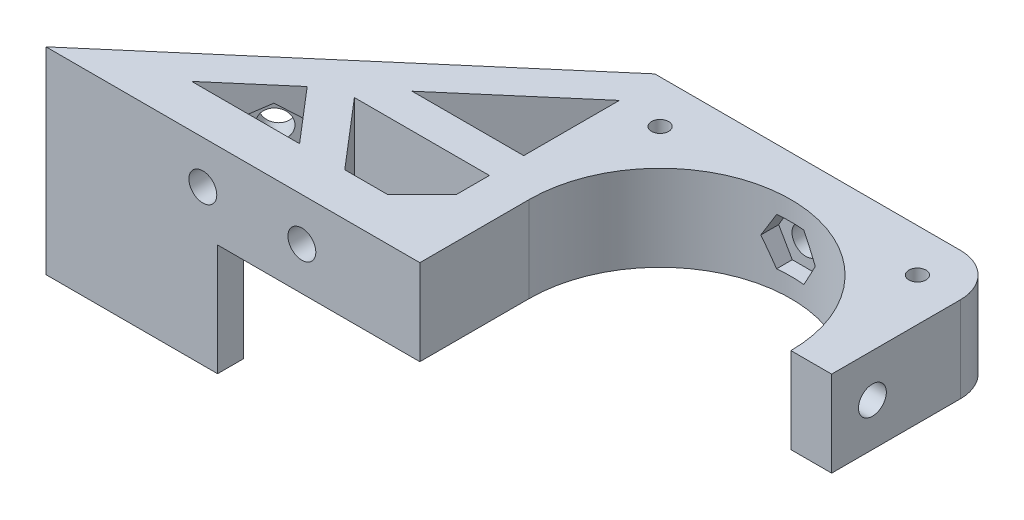
SolidWorks part; units mm, degrees
ref_plane "Alzado" through (0, 0, 0) normal (0, 0, 1) x (1, 0, 0)
ref_plane "Planta" through (0, 0, 0) normal (0, 1, 0) x (1, 0, 0)
ref_plane "Vista lateral" through (0, 0, 0) normal (1, 0, 0) x (0, 0, -1)
sketch "Croquis1" plane through (0, 0, 0) normal (0, 1, 0) x (1, 0, 0)
  line L0 (0, 20) -> (0, -20) construction
  line L1 (-20, 20) -> (20, 20)
  line L2 (-20, 20) -> (-20, -20)
  line L3 (-20, -20) -> (20, -20)
  line L4 (20, 20) -> (20, -20)
  line L5 (-20, 20) -> (20, -20) construction
  line L6 (-20, -20) -> (20, 20) construction
  line L7 (-20, -4.25) -> (-30, -7.25)
  line L8 (-30, -7.25) -> (-30, -15.25)
  line L9 (-30, -15.25) -> (30, -15.25)
  line L10 (20, -4.25) -> (30, -7.25)
  line L11 (30, -7.25) -> (30, -15.25)
  circle A0 centre (-15, 15) radius 2.125
  circle A1 centre (15, 15) radius 2.125
  circle A4 centre (0, 0) radius 15.25
  circle A5 centre (-15, -15) radius 2.125 [skipped]
  circle A6 centre (15, -15) radius 2.125 [skipped]
  point P0 (0, 0)
  point P25 (0, -15.25)
  dimension "D3" = 4.25
  dimension "D7" = 30.5
  dimension "D1" = 40
  dimension "D2" = 40
  dimension "D4" = 5
  dimension "D5" = 2
  dimension "D8" = 8
  dimension "D9" = 10
  dimension "D10" = 15.25
  dimension "D12" = 3
  dimension "D6" = 2
extrude "Soporte caja reductora" add sketch "Croquis1" against normal blind 20
sketch "Croquis3" plane through (0, 0, 15.25) normal (0, 0, 1) x (1, 0, 0)
  line L3 (-20, -20) -> (-20, 0) construction
  circle A0 centre (-23.5, -10) radius 2.125
  circle A1 centre (23.5, -10) radius 2.125
  dimension "D1" = 4.25
  dimension "D2" = 3.5
extrude "Cortar-Extruir1" cut sketch "Croquis3" against normal through all
fillet "Redondeo1" radius 5 2 edges at (-20, -10, -20) (20, -10, -20)
sketch "Sketch1" plane through (0, 0, 0) normal (0, 1, 0) x (1, 0, 0)
  line L0 (15, 20) -> (30, 20)
  line L1 (30, 20) -> (30, 8)
  line L2 (30, 8) -> (25.5, 8)
  line L4 (25.5, 8) -> (25.5, 15)
  line L5 (25.5, 15) -> (20, 15)
  circle A0 centre (15, 15) radius 5
  arc M37 (20, 15) -> (15, 20) centre (15, 15) ccw
  dimension "D1" = 12
  dimension "D2" = 5.5
extrude "Boss-Extrude1" add sketch "Sketch1" along direction (0, 1, 0) on the side against the normal up to surface (20 mm away) contours L5 L4 L2 L1 L0 M37
sketch "Sketch2" plane through (0, 0, -20) normal (0, 0, -1) x (-1, 0, 0)
  line L1 (-20, -20) -> (-20, 0) construction
  circle A0 centre (-22.75, -10) radius 1.625
  dimension "D1" = 3.25
  dimension "D2" = 2.75
extrude "Cut-Extrude1" cut sketch "Sketch2" against normal up to next
sketch "Sketch3" plane through (0, 0, -15) normal (0, 0, 1) x (1, 0, 0)
  line L1 (20, -11.5877) -> (22.75, -13.1754)
  line L2 (22.75, -13.1754) -> (25.5, -11.5877)
  line L3 (25.5, -11.5877) -> (25.5, -8.4123)
  line L4 (25.5, -8.4123) -> (22.75, -6.8246)
  line L5 (22.75, -6.8246) -> (20, -8.4123)
  line L6 (20, -8.4123) -> (20, -11.5877)
  circle A0 centre (22.75, -10) radius 2.75 construction
  dimension "D1" = 5.5
extrude "Cut-Extrude2" cut sketch "Sketch3" against normal blind 2
sketch "Sketch4" plane through (25.5, 0, 0) normal (-1, 0, 0) x (0, 0, 1)
  line L5 (-15, -8.4123) -> (-15, 0) construction
  line L6 (-20, 0) -> (-8, 0) construction
  circle A0 centre (-12.25, -10) radius 1.625
  dimension "D1" = 2.75
  dimension "D2" = 3.25
  dimension "D3" = 10
extrude "Cut-Extrude3" cut sketch "Sketch4" against normal through all
sketch "Sketch5" plane through (30, 0, 0) normal (1, 0, 0) x (0, 0, -1)
  line L1 (15, -11.5877) -> (15, -8.4123)
  line L2 (15, -8.4123) -> (12.25, -6.8246)
  line L3 (12.25, -6.8246) -> (9.5, -8.4123)
  line L4 (9.5, -8.4123) -> (9.5, -11.5877)
  line L5 (9.5, -11.5877) -> (12.25, -13.1754)
  line L6 (12.25, -13.1754) -> (15, -11.5877)
  circle A0 centre (12.25, -10) radius 2.75 construction
  dimension "D1" = 5.5
extrude "Cut-Extrude4" cut sketch "Sketch5" along normal blind 2 from surface
sketch "Croquis6" plane through (0, 0, 0) normal (0, 1, 0) x (1, 0, 0)
  line L0 (-20, -20) -> (20, -20) construction
  line L1 (-15.25, 0) -> (15.25, 0)
  line L2 (-15.25, 0) -> (-15.25, -20)
  line L3 (-15.25, -20) -> (15.25, -20)
  line L4 (15.25, 0) -> (15.25, -20)
  line L6 (-20, -20) -> (20, -20)
  line L7 (-20, -20) -> (-20, -15.25)
  line L8 (-20, -15.25) -> (20, -15.25)
  line L9 (20, -20) -> (20, -15.25)
  circle A0 centre (0, 0) radius 15.25 construction
  circle M5 centre (0, 0) radius 15.25
  line M14 (-20, -15.25) -> (-20, -20)
  line M15 (-20, -20) -> (20, -20)
  line M16 (20, -20) -> (20, -15.25)
extrude "Cortar-Extruir17" cut sketch "Croquis6" against normal through all contours L8 L2 L4 M15 | L8 L2 M14 M15 | L2 L8 M5 | L8 L4 M5 | L8 L4 M15 M16
mirror "Simetría1" about plane through (0, 0, 0) normal (0, 1, 0) of bodies 111
sketch "Croquis7" plane through (0, 0, -20) normal (0, 0, -1) x (-1, 0, 0)
  line L1 (-30, 0) -> (30, 0)
  line L2 (-30, 0) -> (-30, -20)
  line L3 (-30, -20) -> (30, -20)
  line L4 (30, 0) -> (30, -20)
extrude "Cortar-Extruir18" cut sketch "Croquis7" against normal through all
sketch "Croquis8" plane through (0, 20, 0) normal (0, 1, 0) x (1, 0, 0)
  line L3 (-15, 20) -> (30, 20) construction
  line L4 (-11.0405, 13.9391) -> (-10.3152, 11.2321)
  line L5 (10.8174, 13.8793) -> (10.3152, 11.2321)
  line L59 (10.8174, 13.8793) -> (11.9787, 20)
  line L60 (-11.0405, 13.9391) -> (-12.6645, 20)
  line L61 (11.9787, 20) -> (-12.6645, 20)
  circle A0 centre (0, 0) radius 15.25
extrude "Saliente-Extruir2" add sketch "Croquis8" along normal blind 49
sketch "Croquis9" plane through (0, 69, 0) normal (0, 1, 0) x (1, 0, 0)
  line L0 (-20, 0) -> (20, 0)
  line L1 (-20, 15) -> (-20, -4.25) construction
  line L2 (20, 15) -> (20, -4.25) construction
  line L3 (-20, 0) -> (-20, 15)
  line L4 (-15, 20) -> (12.6645, 20)
  line L5 (12.6645, 20) -> (20, 13.9368)
  line L6 (20, 13.9368) -> (20, 0)
  line L7 (20, 0) -> (20.1759, -0.147)
  line L8 (-14.75, 0) -> (-14.75, -15.25)
  line L9 (-15.25, -15.25) -> (-30, -15.25)
  line L10 (-30, -15.25) -> (-30, -7.25)
  line L11 (-30, -7.25) -> (-20, -4.25)
  line L12 (-20, -4.25) -> (-20, 0)
  line L13 (-14.75, -15.25) -> (-15.25, -15.25)
  line L14 (-14.75, -15.25) -> (0, -15.25)
  line L15 (0, -15.25) -> (0, -14.75)
  circle A0 centre (0, 0) radius 14.75
  circle A1 centre (-15, 15) radius 5
  dimension "D1" = 29.5
extrude "Soporte motor" add sketch "Croquis9" against normal blind 15 from offset 15 offset against normal yes
sketch "Croquis12" plane through (0, 0, 15.25) normal (0, 0, 1) x (1, 0, 0)
  line L1 (0, 54) -> (-30, 54) construction
  line L2 (-20, 39) -> (-20, 54) construction
  circle A0 centre (-23.5, 46.5) radius 2.125
  dimension "D3" = 4.25
  dimension "D1" = 7.5
  dimension "D2" = 3.5
extrude "Agujeros de sujecion a base" cut sketch "Croquis12" against normal through all
sketch "Croquis13" plane through (0, 0, 15.25) normal (0, 0, 1) x (1, 0, 0)
  line L1 (-20, 44.4793) -> (-20, 48.5207)
  line L2 (-20, 48.5207) -> (-23.5, 50.5415)
  line L3 (-23.5, 50.5415) -> (-27, 48.5207)
  line L4 (-27, 48.5207) -> (-27, 44.4793)
  line L5 (-27, 44.4793) -> (-23.5, 42.4585)
  line L6 (-23.5, 42.4585) -> (-20, 44.4793)
  circle A0 centre (-23.5, 46.5) radius 3.5 construction
  dimension "D1" = 7
extrude "Tuerca Agujero de sujecion a base" cut sketch "Croquis13" against normal blind 10 from offset 4 offset against normal yes
sketch "Croquis10" plane through (0, 69, 0) normal (0, 1, 0) x (1, 0, 0)
  line L0 (-10.3152, 11.2321) -> (-9.8079, 9.3388)
  line L1 (10.3152, 11.2321) -> (9.4813, 8.1201)
  circle A0 centre (0, 0) radius 14.75
  circle A1 centre (0, 0) radius 15.25
  arc M2 (-10.3152, 11.2321) -> (10.3152, 11.2321) centre (0, 0) cw
extrude "Saliente-Extruir4" add sketch "Croquis10" against normal up to surface (15 mm away) contours A0 L1 L0 M2
sketch "Croquis11" plane through (0, 0, 0) normal (0, -1, 0) x (1, 0, 0)
  line L0 (0, 0) -> (0, -12.6937) construction
  line L1 (15, -20) -> (30, -20)
  line L2 (30, -20) -> (30, 15.25)
  line L3 (30, 15.25) -> (15.25, 15.25)
  line L4 (15.25, 0) -> (15.25, 15.25) construction
  line L5 (15.25, 15.25) -> (30, 15.25) construction
  line L6 (15.25, 15.25) -> (15.25, 4.25)
  line L7 (15.25, 4.25) -> (20, 4.25)
  line L8 (20, 4.25) -> (20, -15)
  circle A0 centre (0, 0) radius 22.5
  circle A1 centre (-15, -15) radius 5
  circle A2 centre (15, -15) radius 5
  line M8 (-15, -20) -> (30, -20)
  line M9 (30, -20) -> (30, -8)
  line M10 (30, -8) -> (25.5, -8)
  line M11 (25.5, -8) -> (25.5, -15)
  line M12 (25.5, -15) -> (20, -15)
  line M14 (20, 4.25) -> (30, 7.25)
  line M15 (30, 7.25) -> (30, 15.25)
  line M16 (30, 15.25) -> (15.25, 15.25)
  line M17 (15.25, 15.25) -> (15.25, 0)
  dimension "D1" = 45
extrude "Cortar-Extruir19" cut sketch "Croquis11" against normal blind 25 contours A0 L3 L7 M14 M17 | A0 M14 M15 M16 | A2 M12 M8 M9 M10 M11
mirror "Simetría2"
sketch "Croquis14" plane through (0, 0, 15.25) normal (0, 0, 1) x (1, 0, 0)
  line L1 (-30, 20) -> (20, 20)
  line L2 (-30, 20) -> (-30, 138)
  line L3 (-30, 138) -> (20, 138)
  line L4 (20, 20) -> (20, 138)
extrude "Cortar-Extruir22" cut sketch "Croquis14" against normal through all
sketch "Croquis15" plane through (0, 0, 0) normal (0, -1, 0) x (1, 0, 0)
  line L0 (-30, 7.25) -> (-30, 15.25) construction
  line L1 (-20, 4.25) -> (-30, 4.25)
  line L2 (-20, 4.25) -> (-20, 11.25)
  line L3 (-20, 11.25) -> (-30, 11.25)
  line L4 (-30, 4.25) -> (-30, 11.25)
  line L5 (-30, 15.25) -> (-15.25, 15.25) construction
  dimension "D1" = 4
extrude "Cortar-Extruir23" cut sketch "Croquis15" against normal through all
sketch "Croquis16" plane through (0, 0, 0) normal (0, -1, 0) x (1, 0, 0)
  line L0 (-15.25, 0) -> (-15.25, 15.25) construction
  line L1 (-30, 15.25) -> (-15.25, 15.25)
  line L2 (-30, 15.25) -> (-30, 12.75)
  line L3 (-20, 12.75) -> (-15.25, 12.75)
  line L4 (-15.25, 15.25) -> (-15.25, 12.75)
  line L5 (-30, 12.75) -> (-30, 11.25)
  line L6 (-30, 11.25) -> (-20, 11.25)
  line L7 (-20, 11.25) -> (-30, 11.25) construction
  line L8 (-20, -15) -> (-20, 11.25) construction
  line L9 (-20, 11.25) -> (-20, 12.75)
  dimension "D1" = 2.5
extrude "Cortar-Extruir24" cut sketch "Croquis16" against normal through all
sketch "Croquis18" plane through (0, 0, -20) normal (0, 0, -1) x (-1, 0, 0)
  line L0 (20, 0) -> (20, 20) construction
  line L1 (-20, 0) -> (20, 0)
  line L2 (-20, 0) -> (-20, 10)
  line L3 (-20, 10) -> (20, 10)
  line L4 (20, 0) -> (20, 10)
  line L5 (15, 20) -> (-15, 20) construction
  dimension "D1" = 10
extrude "Cortar-Extruir25" cut sketch "Croquis18" against normal through all
sketch "Croquis19" plane through (0, 20, 0) normal (0, 1, 0) x (1, 0, 0)
  line L0 (-20, -12.75) -> (-34, -12.75)
  line L1 (-34, -12.75) -> (-34, -7.75)
  line L2 (-34, -7.75) -> (-24, -7.75)
  line L3 (-24, -7.75) -> (-20, -3.75)
  line L4 (-20, 15) -> (-20, -12.75) construction
  line L5 (-20, -3.75) -> (-20, -12.75)
  dimension "D1" = 5
  dimension "D2" = 4
  dimension "D3" = 4
  dimension "D4" = 10
extrude "Saliente-Extruir5" add sketch "Croquis19" against normal up to surface (10 mm away) up to face at (15, 10, -12.875)
sketch "Croquis20" plane through (0, 0, 7.75) normal (0, 0, -1) x (-1, 0, 0)
  circle A0 centre (29, 15) radius 1
  dimension "D1" = 2
extrude "Cortar-Extruir26" cut sketch "Croquis20" against normal through all
sketch "Croquis21" plane through (20, 0, 0) normal (1, 0, 0) x (0, 0, -1)
  line L1 (20, 20) -> (20, 10) construction
  circle A0 centre (4.75, 15) radius 1.625
  dimension "D1" = 3.25
  dimension "D2" = 15.25
extrude "Cortar-Extruir27" cut sketch "Croquis21" against normal up to next
sketch "Croquis22" plane through (0, 10, 0) normal (0, -1, 0) x (1, 0, 0)
  circle A0 centre (-15, -15) radius 2.125
  circle A1 centre (15, -15) radius 2.125
  circle A2 centre (15, -15) radius 1
  circle A3 centre (-15, -15) radius 1
  dimension "D1" = 2
extrude "Saliente-Extruir6" add sketch "Croquis22" against normal blind 10
sketch "Croquis23" plane through (0, 0, -20) normal (0, 0, -1) x (-1, 0, 0)
  circle A0 centre (0, 15) radius 1.625
  dimension "D1" = 3.25
extrude "Cortar-Extruir28" cut sketch "Croquis23" against normal through all
sketch "Croquis24" plane through (0, 0, -20) normal (0, 0, -1) x (-1, 0, 0)
  line L1 (1.5877, 12.25) -> (3.1754, 15)
  line L2 (3.1754, 15) -> (1.5877, 17.75)
  line L3 (1.5877, 17.75) -> (-1.5877, 17.75)
  line L4 (-1.5877, 17.75) -> (-3.1754, 15)
  line L5 (-3.1754, 15) -> (-1.5877, 12.25)
  line L6 (-1.5877, 12.25) -> (1.5877, 12.25)
  circle A0 centre (0, 15) radius 2.75 construction
  dimension "D1" = 5.5
extrude "Cortar-Extruir29" cut sketch "Croquis24" against normal blind 10 from offset 3 offset against normal yes
sketch "Croquis26" plane through (0, 10, 0) normal (0, -1, 0) x (1, 0, 0)
  line L0 (-29, 12.75) -> (-58.825, 12.75)
  line L1 (-58.825, 12.75) -> (-39.1605, -4.1045)
  line L3 (-39.5945, 1.5357) -> (-46.8449, 7.75)
  line L4 (-46.8449, 7.75) -> (-34.2682, 7.75)
  line L5 (-34.2682, 7.75) -> (-39.5945, 1.5357)
  line L7 (-29, 7.75) -> (-35.7321, -0.1045)
  line L8 (-29, 7.75) -> (-29, 12.75)
  line L9 (-34, 7.75) -> (-24, 7.75) construction
  line L10 (-34, 12.75) -> (-15.25, 12.75) construction
  line L11 (-39.1605, -4.1045) -> (-20, -4.1045)
  line L12 (-20, 3.75) -> (-20, -15) construction
  line L13 (-20, -4.1045) -> (-20, -0.1045)
  line L14 (-20, -0.1045) -> (-35.7321, -0.1045)
  dimension "D1" = 4
  dimension "D2" = 4
  dimension "D3" = 4
  dimension "D4" = 29.825
  dimension "D5" = 40.6
extrude "Saliente-Extruir7" add sketch "Croquis26" against normal blind 10
sketch "Croquis27" plane through (0, 0, 12.75) normal (0, 0, 1) x (1, 0, 0)
  line L0 (-29, 16) -> (-29, 14) construction
  line L1 (-46.8449, 20) -> (-46.8449, 10) construction
  circle A0 centre (-40.5449, 15) radius 1.625
  circle A2 centre (-29, 15) radius 1.625
  dimension "D1" = 3.25
  dimension "D2" = 6.3
extrude "Cortar-Extruir30" cut sketch "Croquis27" against normal up to next
sketch "Croquis28" plane through (0, 0, 12.75) normal (0, 0, 1) x (1, 0, 0)
  line L1 (-38.9572, 12.25) -> (-37.3694, 15)
  line L2 (-37.3694, 15) -> (-38.9572, 17.75)
  line L3 (-38.9572, 17.75) -> (-42.1326, 17.75)
  line L4 (-42.1326, 17.75) -> (-43.7203, 15)
  line L5 (-43.7203, 15) -> (-42.1326, 12.25)
  line L6 (-42.1326, 12.25) -> (-38.9572, 12.25)
  line L7 (-27.4123, 12.25) -> (-25.8246, 15)
  line L8 (-25.8246, 15) -> (-27.4123, 17.75)
  line L9 (-27.4123, 17.75) -> (-30.5877, 17.75)
  line L10 (-30.5877, 17.75) -> (-32.1754, 15)
  line L11 (-32.1754, 15) -> (-30.5877, 12.25)
  line L12 (-30.5877, 12.25) -> (-27.4123, 12.25)
  circle A0 centre (-40.5449, 15) radius 2.75 construction
  circle A1 centre (-29, 15) radius 2.75 construction
  dimension "D1" = 5.5
extrude "Cortar-Extruir31" cut sketch "Croquis28" against normal up to next from offset 3 offset against normal yes
sketch "Croquis29" plane through (-18.6128, 0, -21.716) normal (-0.6508, 0, -0.7593) x (-0.7593, 0, 0.6508)
  line L2 (31.0624, 20) -> (31.0624, 10) construction
  circle A0 centre (33.8124, 15) radius 1.625
  dimension "D2" = 3.25
  dimension "D1" = 2.75
extrude "Cortar-Extruir32" cut sketch "Croquis29" against normal up to next
sketch "Croquis31" plane through (-18.6128, 0, -21.716) normal (-0.6508, 0, -0.7593) x (-0.7593, 0, 0.6508)
  line L1 (36.5624, 16.5877) -> (33.8124, 18.1754)
  line L2 (33.8124, 18.1754) -> (31.0624, 16.5877)
  line L3 (31.0624, 16.5877) -> (31.0624, 13.4123)
  line L4 (31.0624, 13.4123) -> (33.8124, 11.8246)
  line L5 (33.8124, 11.8246) -> (36.5624, 13.4123)
  line L6 (36.5624, 13.4123) -> (36.5624, 16.5877)
  circle A0 centre (33.8124, 15) radius 2.75 construction
  dimension "D1" = 5.5
extrude "Cortar-Extruir33" cut sketch "Croquis31" against normal up to next from offset 2.5 offset against normal yes
sketch "Croquis35" plane through (0, 20, 0) normal (0, 1, 0) x (1, 0, 0)
  line L0 (-15, 20) -> (15, 20) construction
  line L1 (10.3896, 0) -> (23.695, 0)
  line L2 (10.3896, 0) -> (10.3896, -6.8269)
  line L3 (10.3896, -6.8269) -> (23.695, -6.8269)
  line L4 (23.695, 0) -> (23.695, -6.8269)
  dimension "D1" = 20
extrude "Cortar-Extruir34" cut sketch "Croquis35" against normal through all both and the other way through all
sketch "Croquis36" plane through (20, 0, 0) normal (1, 0, 0) x (0, 0, -1)
  line L1 (7.5, 16.5877) -> (4.75, 18.1754)
  line L2 (4.75, 18.1754) -> (2, 16.5877)
  line L3 (2, 16.5877) -> (2, 13.4123)
  line L4 (2, 13.4123) -> (4.75, 11.8246)
  line L5 (4.75, 11.8246) -> (7.5, 13.4123)
  line L6 (7.5, 13.4123) -> (7.5, 16.5877)
  circle A0 centre (4.75, 15) radius 2.75 construction
  dimension "D1" = 5.5
extrude "Cortar-Extruir35" cut sketch "Croquis36" against normal blind 10 from offset 3 offset against normal yes
sketch "Croquis37" plane through (0, 10, 0) normal (0, -1, 0) x (1, 0, 0)
  line L0 (-39.1605, -4.1045) -> (-20.6149, -20)
  line L1 (-20.6149, -20) -> (-15, -20)
  line L2 (-33.014, -4.1045) -> (-19.5581, -15.6376)
  line L3 (-39.1605, -4.1045) -> (-20, -4.1045) construction
  line L4 (-19.5581, -15.6376) -> (-15, -20)
  line L5 (-58.825, 12.75) -> (-39.1605, -4.1045) construction
  line L6 (-39.5945, 1.5357) -> (-46.8449, 7.75) construction
  line L7 (-39.1605, -4.1045) -> (-33.014, -4.1045)
extrude "Saliente-Extruir8" add sketch "Croquis37" against normal blind 10
sketch "Croquis38" plane through (0, 10, 0) normal (0, -1, 0) x (1, 0, 0)
  line L0 (-58.825, 12.75) -> (-38.825, 12.75)
  line L1 (-58.825, 12.75) -> (-15.25, 12.75) construction
  line L2 (-38.825, 12.75) -> (-38.825, 9.75)
  line L3 (-38.825, 9.75) -> (-55.3248, 9.75)
  line L4 (-58.825, 12.75) -> (-20.6149, -20) construction
  line L5 (-55.3248, 9.75) -> (-58.825, 12.75)
  dimension "D1" = 3
  dimension "D2" = 20
extrude "Saliente-Extruir9" add sketch "Croquis38" along normal blind 13
sketch "Croquis39" plane through (0, 10, 0) normal (0, -1, 0) x (1, 0, 0)
  line L0 (-38.825, 9.75) -> (-38.825, 7.75)
  line L1 (-46.8449, 7.75) -> (-34.2682, 7.75) construction
  line L3 (-55.3248, 9.75) -> (-20.6149, -20) construction
  line L4 (-52.9914, 7.75) -> (-55.3248, 9.75)
  line L5 (-55.3248, 9.75) -> (-38.825, 9.75)
  line L6 (-52.9914, 7.75) -> (-50.658, 5.75)
  line L7 (-50.658, 5.75) -> (-38.825, 5.75)
  line L8 (-38.825, 5.75) -> (-38.825, 7.75)
  point P5 (0, 0)
  dimension "D1" = 2
extrude "Saliente-Extruir10" add sketch "Croquis39" along normal blind 3
